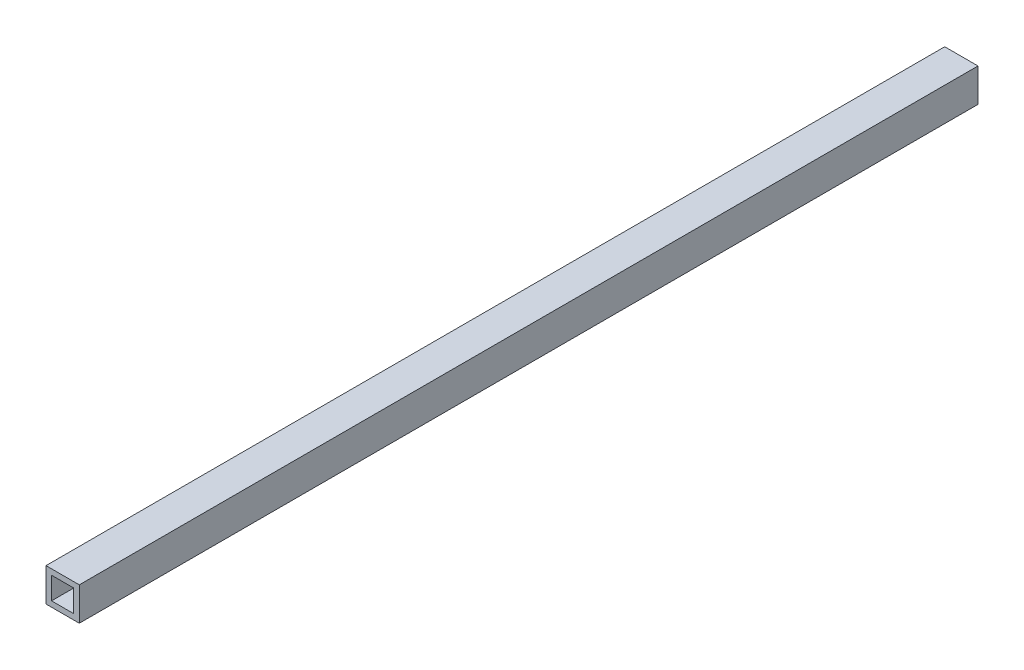
SolidWorks part; units mm, degrees
ref_plane "Front Plane" through (0, 0, 0) normal (0, 0, 1) x (1, 0, 0)
ref_plane "Top Plane" through (0, 0, 0) normal (0, 1, 0) x (1, 0, 0)
ref_plane "Right Plane" through (0, 0, 0) normal (1, 0, 0) x (0, 0, -1)
sketch "Sketch1" plane through (0, 0, 0) normal (0, 0, 1) x (1, 0, 0)
  line L1 (-9.525, -9.525) -> (9.525, -9.525)
  line L2 (-9.525, -9.525) -> (-9.525, 9.525)
  line L3 (-9.525, 9.525) -> (9.525, 9.525)
  line L4 (9.525, -9.525) -> (9.525, 9.525)
  line L5 (-9.525, -9.525) -> (9.525, 9.525) construction
  line L6 (-9.525, 9.525) -> (9.525, -9.525) construction
  point P0 (0, 0)
  dimension "D1" = 19.05
  dimension "D2" = 19.05
extrude "Boss-Extrude1" add sketch "Sketch1" against normal blind 514.35
sketch "Sketch2" plane through (0, 0, 0) normal (0, 0, 1) x (1, 0, 0)
  line L1 (-6.35, -6.35) -> (6.35, -6.35)
  line L2 (-6.35, -6.35) -> (-6.35, 6.35)
  line L3 (-6.35, 6.35) -> (6.35, 6.35)
  line L4 (6.35, -6.35) -> (6.35, 6.35)
  line L5 (-6.35, -6.35) -> (6.35, 6.35) construction
  line L6 (-6.35, 6.35) -> (6.35, -6.35) construction
  point P0 (0, 0)
  dimension "D1" = 12.7
  dimension "D2" = 12.7
extrude "Cut-Extrude1" cut sketch "Sketch2" against normal up to next
equation "\"D2@Sketch1\"=\"D1@Sketch1\""
equation "\"D2@Sketch2\"=\"D1@Sketch2\""
